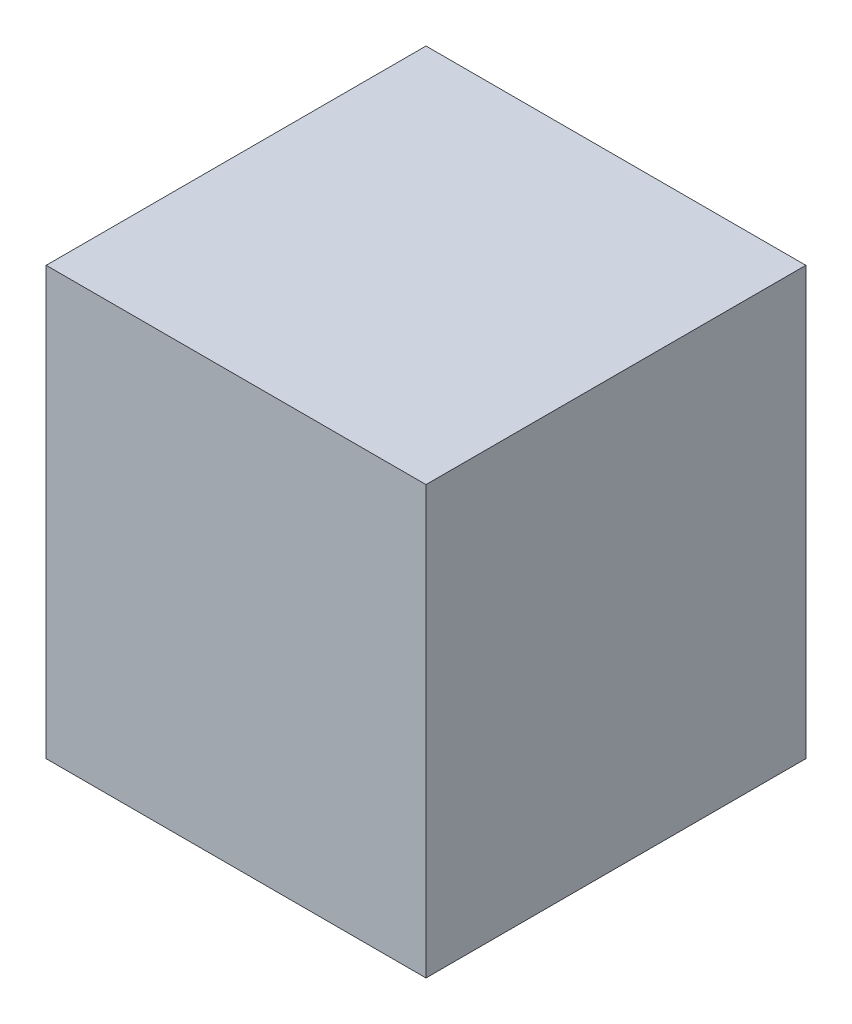
SolidWorks part; units mm, degrees
ref_plane "Front Plane" through (0, 0, 0) normal (0, 0, 1) x (1, 0, 0)
ref_plane "Top Plane" through (0, 0, 0) normal (0, 1, 0) x (1, 0, 0)
ref_plane "Right Plane" through (0, 0, 0) normal (1, 0, 0) x (0, 0, -1)
sketch "Sketch1" plane through (0, 0, 0) normal (0, 1, 0) x (1, 0, 0)
  line L1 (0, 0) -> (-80, 0)
  line L2 (0, 0) -> (0, 80)
  line L3 (0, 80) -> (-80, 80)
  line L4 (-80, 0) -> (-80, 80)
  dimension "D1" = 80
  dimension "D2" = 80
extrude "Extrude1" add sketch "Sketch1" along normal blind 90
